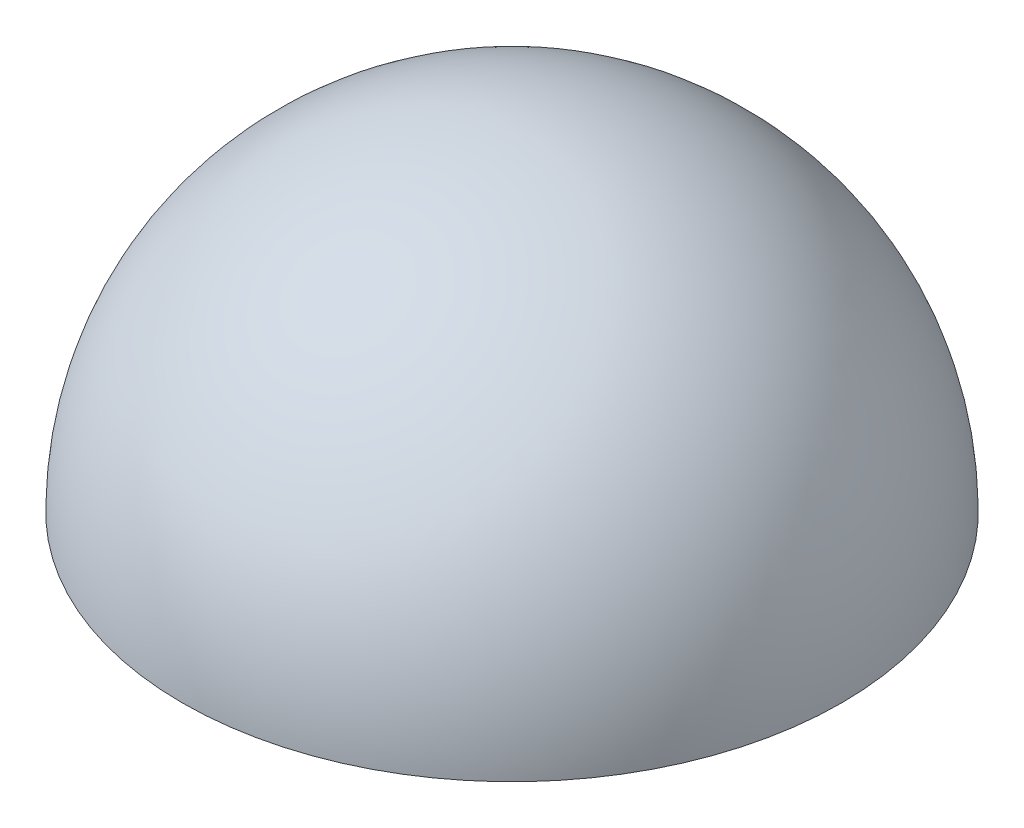
SolidWorks part; units mm, degrees
material "Rubber"
ref_plane "Front Plane" through (0, 0, 0) normal (0, 0, 1) x (1, 0, 0)
ref_plane "Top Plane" through (0, 0, 0) normal (0, 1, 0) x (1, 0, 0)
ref_plane "Right Plane" through (0, 0, 0) normal (1, 0, 0) x (0, 0, -1)
sketch "Sketch1" plane through (0, 0, 0) normal (0, 0, 1) x (1, 0, 0)
  line L0 (0, 20) -> (0, 0)
  line L2 (0, 0) -> (20, 0)
  arc A0 (20, 0) -> (0, 20) centre (0, 0) ccw
  dimension "D1" = 20
  dimension "D2" = 28.2843
  dimension "D3" = 20
revolve "Revolve1" add sketch "Sketch1" angle 360 about L0
